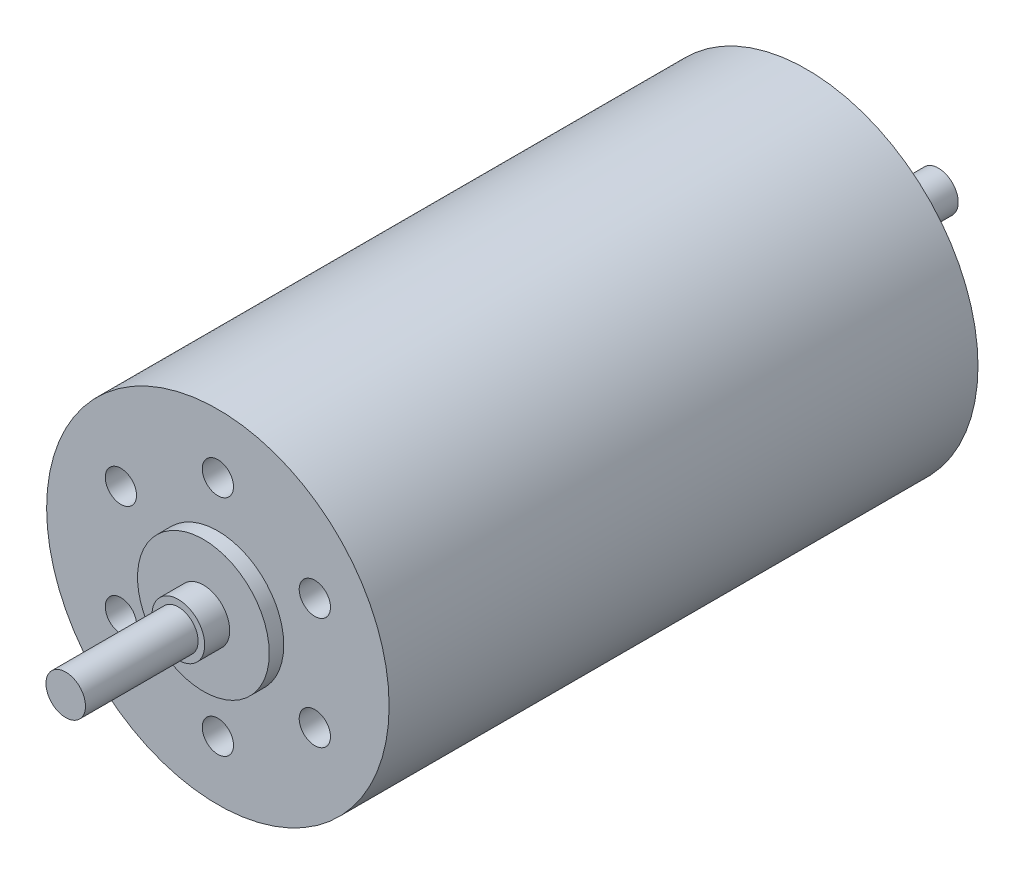
SolidWorks part; units mm, degrees
ref_plane "Front Plane" through (0, 0, 0) normal (1, 0, 0) x (0, 1, 0)
ref_plane "Top Plane" through (0, 0, 0) normal (0, 0, 1) x (0, 1, 0)
ref_plane "Right Plane" through (0, 0, 0) normal (0, 1, 0) x (-1, 0, 0)
sketch "Sketch1" plane through (0, 0, 0) normal (0, 0, 1) x (0, 1, 0)
  circle A0 centre (0, 0) radius 13
  dimension "D1" = 26
extrude "Boss-Extrude1" add sketch "Sketch1" along normal mid plane 44.7
sketch "Sketch2" plane through (0, 0, 22.35) normal (0, 0, 1) x (1, 0, 0)
  circle A0 centre (0, 0) radius 5
  dimension "D1" = 10
extrude "Boss-Extrude2" add sketch "Sketch2" along normal blind 1.1
sketch "Sketch3" plane through (0, 0, 23.45) normal (0, 0, 1) x (1, 0, 0)
  circle A0 centre (0, 0) radius 2
  dimension "D1" = 4
extrude "Boss-Extrude3" add sketch "Sketch3" along normal blind 1.9
sketch "Sketch4" plane through (0, 0, 25.35) normal (0, 0, 1) x (1, 0, 0)
  circle A0 centre (0, 0) radius 1.5
  dimension "D1" = 3
extrude "Boss-Extrude4" add sketch "Sketch4" along normal blind 8.55
sketch "Sketch5" plane through (0, 0, -22.35) normal (0, 0, -1) x (1, 0, 0)
  circle A0 centre (0, 0) radius 4
  dimension "D1" = 8
extrude "Boss-Extrude5" add sketch "Sketch5" along normal blind 2.2
sketch "Sketch6" plane through (0, 0, -24.55) normal (0, 0, -1) x (1, 0, 0)
  circle A0 centre (0, 0) radius 1.5
  dimension "D1" = 3
extrude "Boss-Extrude6" add sketch "Sketch6" along normal blind 7.8
hole_wizard "#42 (0.0935) Diameter Hole1" positions "Sketch8" profile "Sketch9" hole size "#42" standard "ANSI Inch"
sketch "Sketch8" plane through (0, 0, 22.35) normal (0, 0, 1) x (1, 0, 0)
  line L0 (-7.3612, 4.25) -> (7.3612, -4.25) construction
  line L2 (7.3612, 4.25) -> (-7.3612, -4.25) construction
  line L4 (0, 8.5) -> (0, -8.5) construction
  circle A0 centre (0, 0) radius 8.5
  point P0 (7.3612, -4.25)
  point P2 (0, 8.5)
  point P4 (-7.3612, 4.25)
  point P6 (-7.3612, -4.25)
  point P8 (7.3612, 4.25)
  point P10 (0, -8.5)
  dimension "D1" = 17
  dimension "D2" = 60
  dimension "D3" = 60
sketch "Sketch9" plane through (7.3612, -4.25, 22.35) normal (1, 0, 0) x (0, -1, 0)
  line L0 (0, 0) -> (0, 13.4135)
  line L1 (0, 13.4135) -> (1.1874, 12.7)
  line L2 (1.1874, 12.7) -> (1.1874, 0)
  line L5 (1.1874, 0) -> (0, 0)
  line L10 (0, 13.4135) -> (-1.1874, 12.7) construction
  line L11 (0, -6.35) -> (0, 107.95) construction
  dimension "Hole Dia." = 2.3749
  dimension "Hole Depth" = 12.7
  dimension "Drill Angle" = 118
